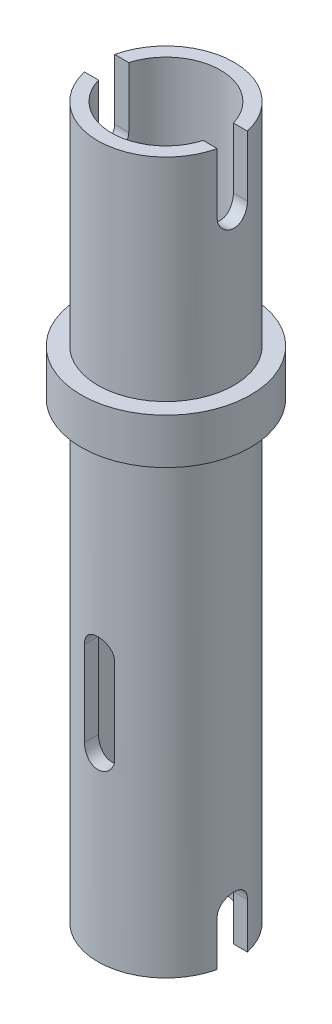
SolidWorks part; units mm, degrees
ref_plane "Front Plane" through (0, 0, 0) normal (0, 0, 1) x (1, 0, 0)
ref_plane "Top Plane" through (0, 0, 0) normal (0, 1, 0) x (1, 0, 0)
ref_plane "Right Plane" through (0, 0, 0) normal (1, 0, 0) x (0, 0, -1)
sketch "Sketch1" plane through (0, 0, 0) normal (0, 1, 0) x (1, 0, 0)
  circle A0 centre (0, 0) radius 2.8
  dimension "D1" = 5.6
extrude "Boss-Extrude1" add sketch "Sketch1" along normal blind 1.5
sketch "Sketch2" plane through (0, 1.5, 0) normal (0, 1, 0) x (1, 0, 0)
  circle A0 centre (0, 0) radius 2.25
  dimension "D1" = 4.5
extrude "Boss-Extrude2" add sketch "Sketch2" along normal blind 7
sketch "Sketch3" plane through (0, 0, 0) normal (0, -1, 0) x (1, 0, 0)
  circle A0 centre (0, 0) radius 2.25
  dimension "D1" = 4.5
extrude "Boss-Extrude3" add sketch "Sketch3" along normal blind 15
ref_plane "Plane1" through (100, 0, 0) normal (1, 0, 0) x (0, 0, -1)
sketch "Sketch4" plane through (100, 0, 0) normal (1, 0, 0) x (0, 0, -1)
  line L0 (0, 0) -> (0, -13.5) construction
  line L1 (0, -13.5) -> (0, -15) construction
  line L2 (-2.25, -15) -> (2.25, -15) construction
  line L3 (0.5, -13.5) -> (0.5, -15)
  line L4 (-0.5, -13.5) -> (-0.5, -15)
  line L5 (0, 1.5) -> (0, 6.5) construction
  line L6 (2.8, 1.5) -> (-2.8, 1.5) construction
  line L7 (0, 6.5) -> (0, 8.5) construction
  line L8 (2.25, 8.5) -> (-2.25, 8.5) construction
  line L9 (-0.5, 6.5) -> (-0.5, 8.5)
  line L10 (0.5, 6.5) -> (0.5, 8.5)
  arc A0 (0.5, -13.5) -> (-0.5, -13.5) centre (0, -13.5) ccw
  arc A1 (-0.5, -15) -> (0.5, -15) centre (0, -15) ccw
  arc A2 (-0.5, 6.5) -> (0.5, 6.5) centre (0, 6.5) ccw
  arc A3 (0.5, 8.5) -> (-0.5, 8.5) centre (0, 8.5) ccw
  point P3 (0, -14.25)
  point P15 (0, 7.5)
extrude "Cut-Extrude1" cut sketch "Sketch4" against normal through all
ref_plane "Plane2" through (0, 100, 0) normal (0, 1, 0) x (1, 0, 0)
sketch "Sketch5" plane through (0, 100, 0) normal (0, 1, 0) x (1, 0, 0)
  circle A0 centre (0, 0) radius 1.8
  dimension "D1" = 3.6
extrude "Cut-Extrude2" cut sketch "Sketch5" against normal through all
ref_plane "Plane3" through (0, 0, 10) normal (0, 0, 1) x (1, 0, 0)
sketch "Sketch6" plane through (0, 0, 10) normal (0, 0, 1) x (1, 0, 0)
  line L0 (0, 0) -> (0, -6.4) construction
  line L1 (0, -15) -> (0, -9) construction
  line L2 (-2.1937, -15) -> (2.1937, -15) construction
  line L3 (0, -9) -> (0, -6.1915) construction
  line L4 (-0.5, -9) -> (-0.5, -6.1915)
  line L5 (0.5, -9) -> (0.5, -6.1915)
  arc A0 (-0.5, -9) -> (0.5, -9) centre (0, -9) ccw
  arc A1 (0.5, -6.1915) -> (-0.5, -6.1915) centre (0, -6.1915) ccw
  point P7 (0, -7.5958)
  dimension "D1" = 6.4
extrude "Cut-Extrude3" cut sketch "Sketch6" against normal through all
